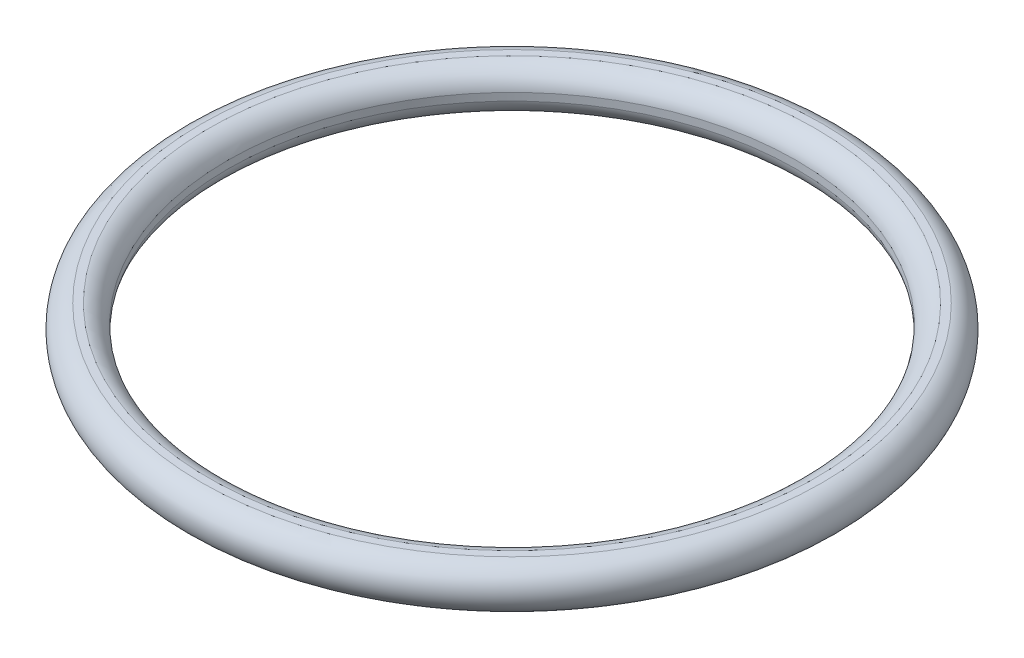
SolidWorks part; units mm, degrees
material "Резина"
ref_plane "Спереди" through (0, 0, 0) normal (0, 0, 1) x (1, 0, 0)
ref_plane "Сверху" through (0, 0, 0) normal (0, 1, 0) x (1, 0, 0)
ref_plane "Справа" through (0, 0, 0) normal (1, 0, 0) x (0, 0, -1)
sketch "Эскиз1" plane through (0, 0, 0) normal (0, 0, 1) x (1, 0, 0)
  line L0 (0, 0) -> (0, 2.4124) construction
  line L1 (0, 0) -> (10.15, 0) construction
  line L2 (9.4105, 0.125) -> (9.4105, -0.125)
  line L4 (10.025, 0.7395) -> (10.275, 0.7395)
  arc A0 (9.4105, -0.125) -> (10.275, 0.7395) centre (10.15, 0) ccw
  arc A1 (10.025, 0.7395) -> (9.4105, 0.125) centre (10.15, 0) ccw
  point P7 (10.15, 0.7395)
  point P10 (9.4105, 0)
  dimension "D1" = 1.5
  dimension "D2" = 10.15
  dimension "D3" = 0.25
revolve "Повернуть1" add sketch "Эскиз1" angle 360 about L0
